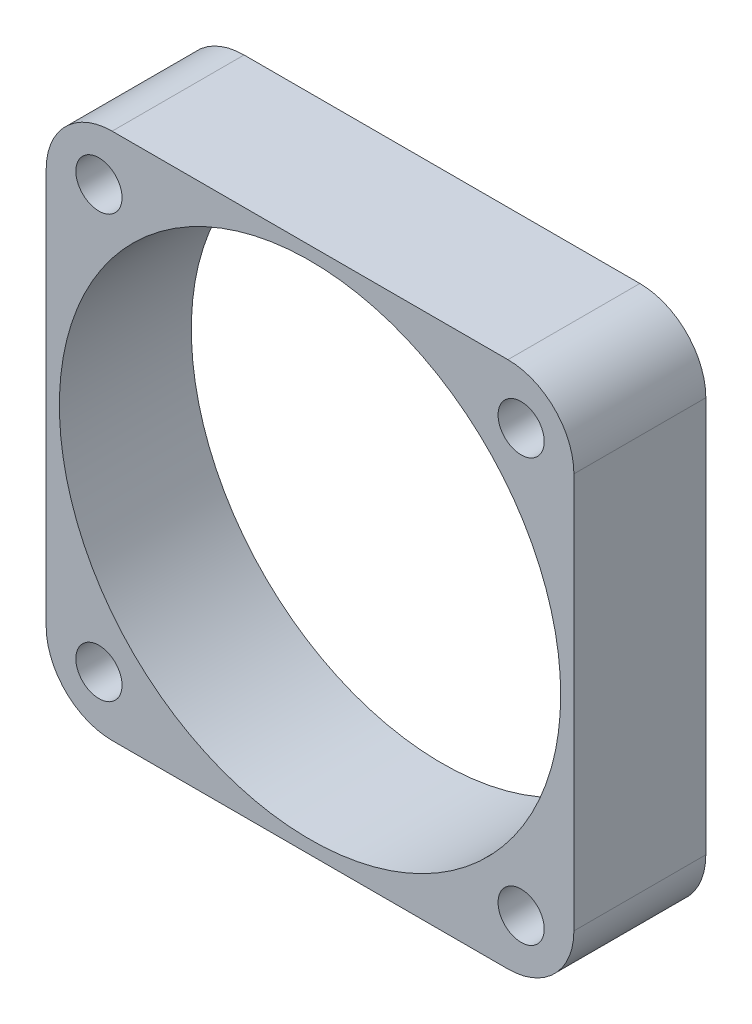
SolidWorks part; units mm, degrees
material "ABS PC"
ref_plane "Front Plane" through (0, 0, 0) normal (0, 0, 1) x (1, 0, 0)
ref_plane "Top Plane" through (0, 0, 0) normal (0, 1, 0) x (1, 0, 0)
ref_plane "Right Plane" through (0, 0, 0) normal (1, 0, 0) x (0, 0, -1)
sketch "Sketch1" plane through (0, 0, 0) normal (0, 0, 1) x (1, 0, 0)
  line L1 (0, 0) -> (40, 0)
  line L2 (0, 0) -> (0, 40)
  line L3 (0, 40) -> (40, 40)
  line L4 (40, 0) -> (40, 40)
  dimension "D1" = 40
  dimension "D2" = 40
extrude "Boss-Extrude1" add sketch "Sketch1" along normal blind 10
sketch "Sketch3" plane through (0, 0, 10) normal (0, 0, 1) x (1, 0, 0)
  line L0 (0, 20) -> (20, 20) construction
  line L1 (0, 40) -> (0, 0) construction
  line L2 (20, 20) -> (20, 0) construction
  line L3 (0, 0) -> (40, 0) construction
  circle A0 centre (20, 20) radius 19
  circle A1 centre (4, 36) radius 1.75
  circle A2 centre (36, 36) radius 1.75
  circle A3 centre (36, 4) radius 1.75
  circle A4 centre (4, 4) radius 1.75
  dimension "D1" = 38
  dimension "D6" = 3.5
  dimension "D2" = 32
  dimension "D3" = 32
  dimension "D4" = 32
  dimension "D5" = 32
extrude "Cut-Extrude1" cut sketch "Sketch3" against normal blind 10 contours A0 | A1 | A4 | A3 | A2
fillet "Fillet1" radius 5 4 edges at (0, 0, 5) (40, 0, 5) (0, 40, 5) (40, 40, 5)
